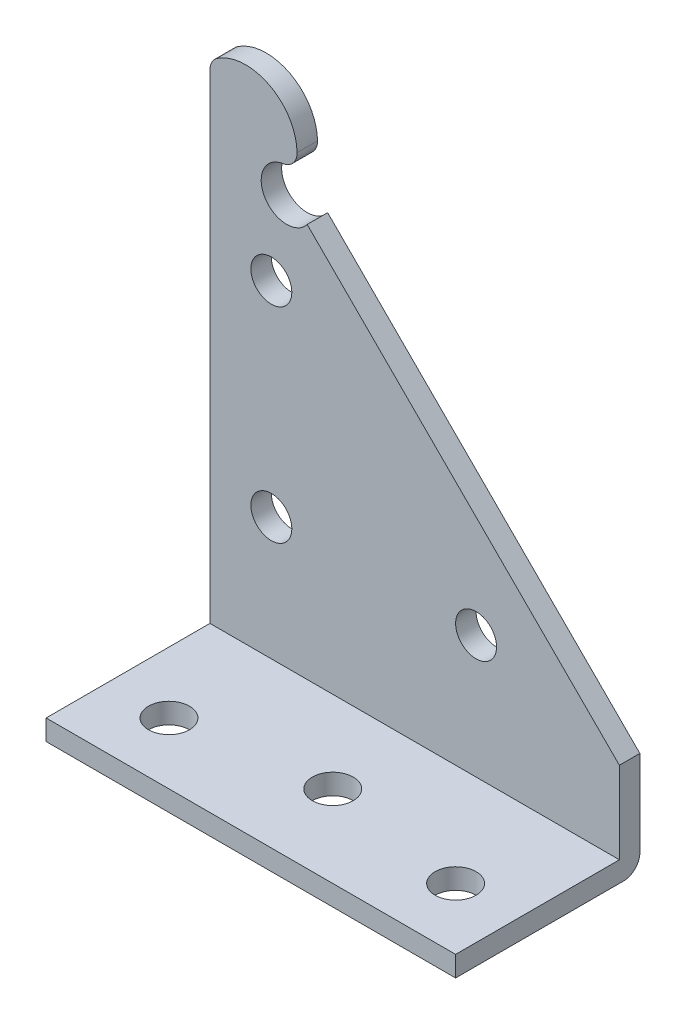
SolidWorks part; units mm, degrees
ref_plane "Front Plane" through (0, 0, 0) normal (0, 0, 1) x (1, 0, 0)
ref_plane "Top Plane" through (0, 0, 0) normal (0, 1, 0) x (1, 0, 0)
ref_plane "Right Plane" through (0, 0, 0) normal (1, 0, 0) x (0, 0, -1)
sketch "Sketch1" plane through (0, 0, 0) normal (0, 0, 1) x (1, 0, 0)
  line L0 (-41.275, 55.2871) -> (-41.275, -22.225)
  line L1 (-41.275, -22.225) -> (22.225, -22.225)
  line L2 (22.225, -22.225) -> (22.225, -6.35)
  line L3 (22.225, -6.35) -> (-26.1947, 42.0697)
  circle A0 centre (0, 0) radius 3.175
  circle A1 centre (-31.75, 0) radius 3.175
  circle A2 centre (-31.75, 31.75) radius 3.175
  arc A4 (-29.9355, 48.3707) -> (-26.1947, 42.0697) centre (-29.3624, 44.45) ccw
  arc A5 (-27.7632, 50.9235) -> (-40.1541, 57.3937) centre (-35.7124, 50.8) ccw
  arc A6 (-41.275, 55.2871) -> (-40.1541, 57.3937) centre (-38.735, 55.2871) cw
  arc A7 (-29.9355, 48.3707) -> (-27.7632, 50.9235) centre (-30.3029, 50.884) ccw
  dimension "D3" = 6.35
  dimension "D13" = 2.54
  dimension "D14" = 7.9248
  dimension "D1" = 31.75
  dimension "D2" = 31.75
  dimension "D4" = 9.525
  dimension "D5" = 63.5
  dimension "D6" = 15.875
  dimension "D7" = 22.225
  dimension "D8" = 45
  dimension "D9" = 5.5626
  dimension "D10" = 6.35
  dimension "D11" = 19.05
  dimension "D12" = 6.35
extrude "Boss-Extrude1" add sketch "Sketch1" along normal blind 3.175
ref_plane "Plane1" through (0, -22.225, 0) normal (0, 1, 0) x (1, 0, 0)
sketch "Sketch2" plane through (0, -22.225, 0) normal (0, 1, 0) x (1, 0, 0)
  line L1 (-41.275, -3.175) -> (22.225, -3.175)
  line L2 (-41.275, -3.175) -> (-41.275, -28.575)
  line L3 (-41.275, -28.575) -> (22.225, -28.575)
  line L4 (22.225, -3.175) -> (22.225, -28.575)
  circle A0 centre (-9.525, -15.875) radius 3.175
  circle A1 centre (-31.75, -19.05) radius 3.175
  circle A2 centre (12.7, -19.05) radius 3.175
  dimension "D2" = 6.35
  dimension "D1" = 25.4
  dimension "D3" = 9.525
  dimension "D4" = 3.175
  dimension "D5" = 9.525
  dimension "D6" = 9.525
  dimension "D7" = 31.75
extrude "Boss-Extrude2" add sketch "Sketch2" along normal blind 3.175
fillet "Fillet1" radius 2.54 1 edges at (-9.525, -22.225, 0)
